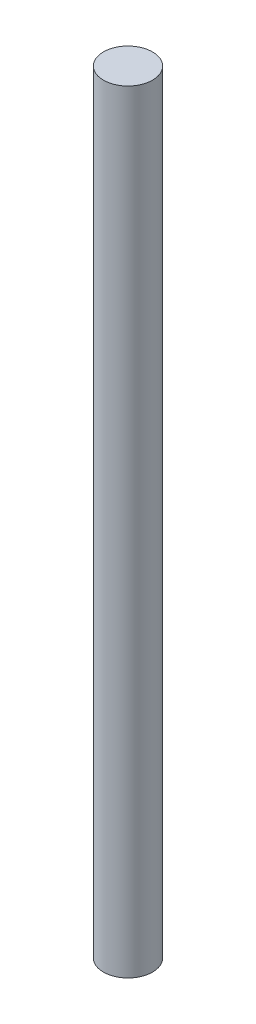
SolidWorks part; units mm, degrees
ref_plane "Front Plane" through (0, 0, 0) normal (0, 0, 1) x (1, 0, 0)
ref_plane "Top Plane" through (0, 0, 0) normal (0, 1, 0) x (1, 0, 0)
ref_plane "Right Plane" through (0, 0, 0) normal (1, 0, 0) x (0, 0, -1)
sketch "Sketch1" plane through (0, 0, 0) normal (0, 1, 0) x (1, 0, 0)
  circle A0 centre (0, 0) radius 4
  dimension "D1" = 8
extrude "Boss-Extrude1" add sketch "Sketch1" along normal blind 126
